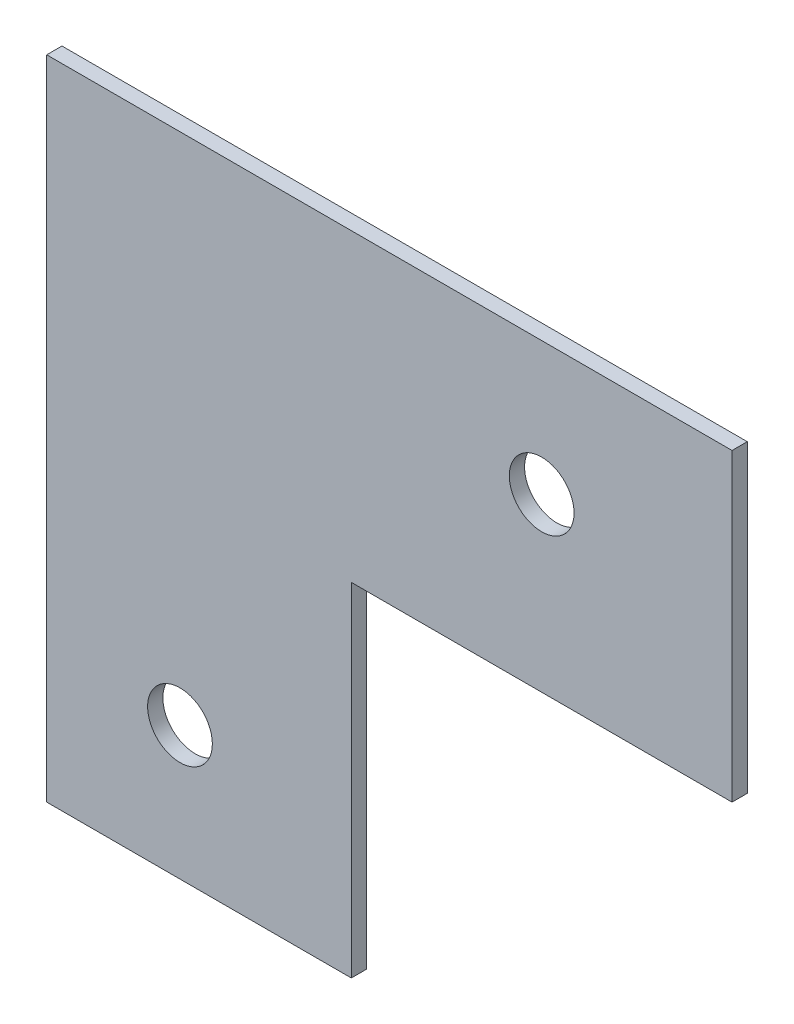
SolidWorks part; units mm, degrees
ref_plane "Front Plane" through (0, 0, 0) normal (0, 0, 1) x (1, 0, 0)
ref_plane "Top Plane" through (0, 0, 0) normal (0, 1, 0) x (1, 0, 0)
ref_plane "Right Plane" through (0, 0, 0) normal (1, 0, 0) x (0, 0, -1)
sketch "Sketch1" plane through (0, 0, 0) normal (0, 0, 1) x (1, 0, 0)
  line L0 (40, 0) -> (40, -45)
  line L1 (90, 0) -> (90, 40)
  line L2 (90, 40) -> (0, 40)
  line L3 (0, 40) -> (0, 0)
  line L4 (40, 0) -> (90, 0)
  line L5 (40, -45) -> (0, -45)
  line L6 (0, -45) -> (0, 0)
  dimension "D1" = 90
  dimension "D2" = 40
  dimension "D3" = 40
extrude "Boss-Extrude1" add sketch "Sketch1" along normal blind 2
sketch "Sketch2" plane through (0, 0, 2) normal (0, 0, 1) x (1, 0, 0)
  line L1 (90, 0) -> (90, 40) construction
  line L2 (90, 40) -> (0, 40) construction
  line L4 (40, 0) -> (90, 0) construction
  line L5 (40, -45) -> (40, 0) construction
  circle A0 centre (17.5, -27.5) radius 4.25
  circle A1 centre (65, 22.5) radius 4.25
  dimension "D1" = 8.5
  dimension "D2" = 22.5
  dimension "D3" = 25
  dimension "D4" = 67.5
  dimension "D5" = 22.5
extrude "Cut-Extrude1" cut sketch "Sketch2" against normal up to next
